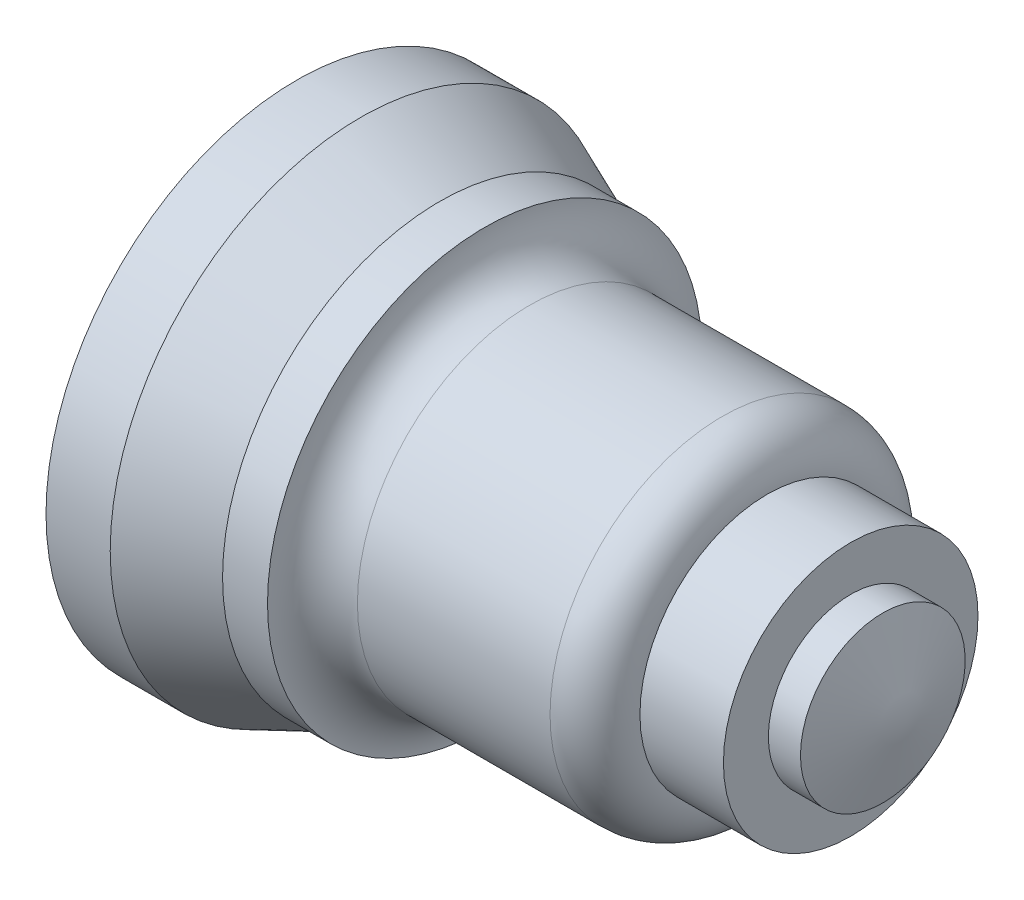
SolidWorks part; units mm, degrees
ref_plane "Front Plane" through (0, 0, 0) normal (0, 0, 1) x (1, 0, 0)
ref_plane "Top Plane" through (0, 0, 0) normal (0, 1, 0) x (1, 0, 0)
ref_plane "Right Plane" through (0, 0, 0) normal (1, 0, 0) x (0, 0, -1)
sketch "Sketch1" plane through (0, 0, 0) normal (0, 0, 1) x (1, 0, 0)
  line L0 (0, 0) -> (120.65, 0)
  line L23 (0, 0) -> (0, 49.53)
  line L30 (0, 49.53) -> (12.7, 49.53)
  line L32 (46.1245, 34.066) -> (84.2245, 34.066)
  line L33 (93.1145, 25.176) -> (109.6245, 25.176)
  line L34 (109.6245, 25.176) -> (109.6245, 16.286)
  line L35 (109.6245, 16.286) -> (115.9745, 16.286)
  line L36 (115.9745, 16.286) -> (120.65, 0)
  line L37 (37.2345, 42.956) -> (28.3445, 42.956)
  line L38 (12.7, 49.53) -> (28.3445, 42.956)
  arc A1 (37.2345, 42.956) -> (46.1245, 34.066) centre (46.1245, 42.956) ccw
  arc A4 (93.1145, 25.176) -> (84.2245, 34.066) centre (84.2245, 25.176) ccw
  dimension "D3" = 11.0255
  dimension "D4" = 49.53
  dimension "D5" = 27.5355
  dimension "D6" = 74.5255
  dimension "D2" = 4.6755
  dimension "D1" = 120.65
  dimension "D7" = 83.4155
  dimension "D8" = 92.3055
  dimension "D9" = 107.95
revolve "Revolve5" add sketch "Sketch1" angle 360 about L0
